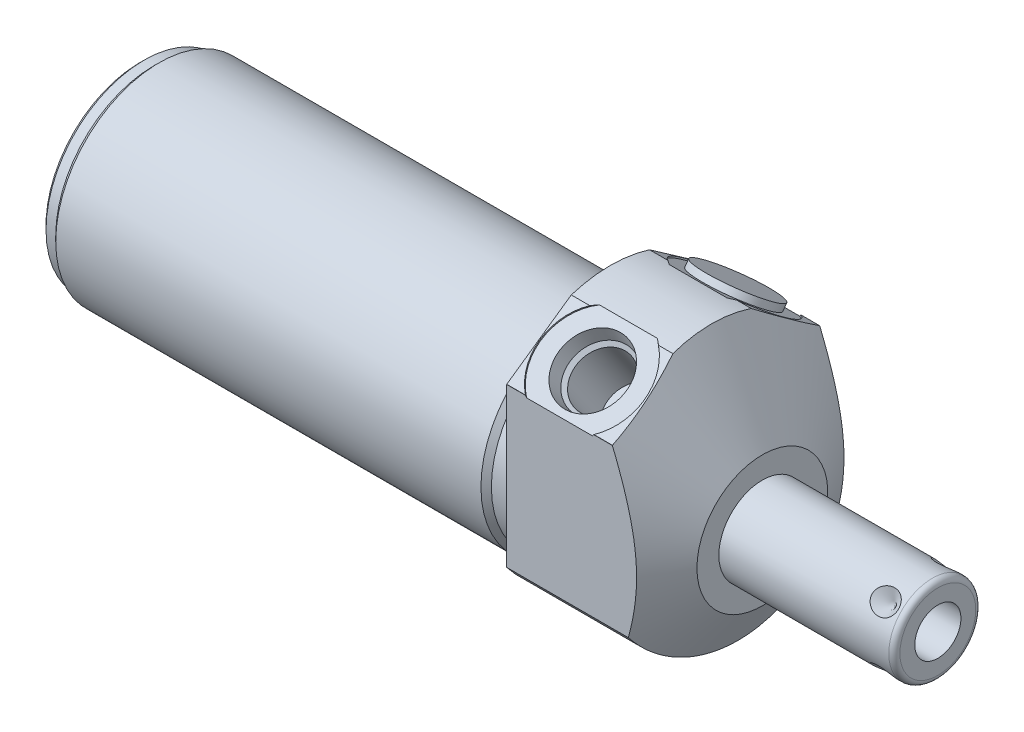
SolidWorks part; units mm, degrees
material "Alloy Steel"
ref_plane "Front Plane" through (0, 0, 0) normal (0, 0, 1) x (1, 0, 0)
ref_plane "Top Plane" through (0, 0, 0) normal (0, 1, 0) x (1, 0, 0)
ref_plane "Right Plane" through (0, 0, 0) normal (1, 0, 0) x (0, 0, -1)
ref_plane "Plane1" through (0, 0, 0) normal (1, 0, 0) x (0, 0, -1)
sketch "Sketch1" plane through (0, 0, 0) normal (1, 0, 0) x (0, 0, -1)
  circle A0 centre (0, 0) radius 23.8125
  dimension "D1" = 47.625
extrude "Extrude1" add sketch "Sketch1" along normal blind 27.7368 and the other way blind 85.852
ref_plane "Plane2" through (0, 0, 0) normal (1, 0, 0) x (0, 0, -1)
sketch "Sketch2" plane through (0, 0, 0) normal (1, 0, 0) x (0, 0, -1)
  line L0 (-20.7455, -4.191) -> (20.7455, -4.191) construction
  circle A0 centre (0, -4.191) radius 18.8595
  circle A1 centre (0, 0) radius 23.8125 construction
  circle A2 centre (0, 0) radius 23.8125
  dimension "D2" = 37.719
  dimension "D1" = 4.191
extrude "Cut-Extrude1" cut sketch "Sketch2" against normal up to next
ref_plane "Plane4" through (0, 0, 0) normal (-1, 0, 0) x (0, 0, 1)
sketch "Sketch4" plane through (0, 0, 0) normal (-1, 0, 0) x (0, 0, 1)
  line L0 (18.923, -14.4553) -> (18.923, 14.4659)
  line L1 (18.923, 14.4659) -> (0, 27.7159)
  line L2 (-18.923, -14.4553) -> (-18.923, 14.4659)
  line L3 (-18.923, 14.4659) -> (0, 27.7159)
  line L4 (0, -26.3889) -> (0, 30.2923) construction
  circle A0 centre (0, 0) radius 28.575
  circle A1 centre (0, 0) radius 23.8125 construction
  arc A3 (-18.923, -14.4553) -> (18.923, -14.4553) centre (0, 0) ccw
  dimension "D4" = 57.15
  dimension "D1" = 37.846
  dimension "D2" = 27.7159
  dimension "D3" = 55
extrude "Cut-Extrude3" cut sketch "Sketch4" against normal up to next
ref_plane "Plane6" through (0, 0, 0) normal (0, 0, 1) x (1, 0, 0)
sketch "Sketch6" plane through (0, 0, 0) normal (0, 0, 1) x (1, 0, 0)
  line L0 (4.7132, 47.625) -> (27.7368, 7.747)
  line L1 (3.6128, -4.191) -> (28.9388, -4.191) construction
  line L2 (-85.852, -4.191) -> (0, -4.191) construction
  line L3 (27.7368, 7.747) -> (27.7368, 47.625)
  line L4 (27.7368, 47.625) -> (4.7132, 47.625)
  line L5 (27.7368, -14.4553) -> (27.7368, 14.4553) construction
  dimension "D1" = 23.876
  dimension "D2" = 30
  dimension "D3" = 39.878
revolve "Cut-Revolve2" cut sketch "Sketch6" angle 360 about L1
ref_plane "Plane7" through (9.652, 18.3948, 12.869) normal (1, 0, 0) x (0, 0.5736, -0.8192)
sketch "S2D0002" plane through (9.652, 18.3948, 12.869) normal (1, 0, 0) x (0, 0.5736, -0.8192)
  line L0 (0, 0) -> (6.1849, 0)
  line L1 (6.1849, 0) -> (5.6423, -2.5527)
  line L2 (5.6423, -2.5527) -> (4.9784, -3.2166)
  line L3 (4.9784, -3.2166) -> (4.9784, -13.462)
  line L4 (4.9784, -13.462) -> (0, -13.462)
  line L5 (0, -13.462) -> (0, 0)
  line L6 (0, -14.1351) -> (0, 0.6731) construction
  dimension "D1" = 13.462
revolve "Cut-Revolve3" cut sketch "S2D0002" angle 360 about L6
ref_plane "Plane8" through (9.652, 18.3948, -12.869) normal (1, 0, 0) x (0, -0.5736, -0.8192)
sketch "Sketch8" plane through (9.652, 18.3948, -12.869) normal (1, 0, 0) x (0, -0.5736, -0.8192)
  line L0 (0, 0) -> (6.1849, 0)
  line L1 (6.1849, 0) -> (5.6423, -2.5527)
  line L2 (5.6423, -2.5527) -> (4.9784, -3.2166)
  line L3 (4.9784, -3.2166) -> (4.9784, -13.462)
  line L4 (4.9784, -13.462) -> (0, -13.462)
  line L5 (0, -13.462) -> (0, 0)
  line L6 (0, -14.1351) -> (0, 0.6731) construction
  dimension "D1" = 13.462
revolve "Cut-Revolve4" cut sketch "Sketch8" angle 360 about L6
sketch "Sketch18" plane through (0, 18.5976, 13.0222) normal (0, 0.8192, 0.5736) x (1, 0, 0)
  circle A0 centre (9.652, 0.0091) radius 9.525
  dimension "D1" = 19.05
extrude "Cut-Extrude4" cut sketch "Sketch18" against normal blind 0.254
sketch "Sketch19" plane through (0, 18.5976, -13.0222) normal (0, 0.8192, -0.5736) x (1, 0, 0)
  circle A0 centre (9.652, -0.0091) radius 9.525
  dimension "D1" = 19.05
extrude "Cut-Extrude5" cut sketch "Sketch19" against normal blind 0.254
ref_plane "Plane10" through (0, 0, 0) normal (0, 0, 1) x (1, 0, 0)
sketch "Sketch10" plane through (0, 0, 0) normal (0, 0, 1) x (1, 0, 0)
  line L0 (0, 14.6685) -> (0, 13.716)
  line L1 (0, 13.716) -> (-3.81, 13.716)
  line L2 (-3.81, 13.716) -> (-4.7625, 14.6685)
  line L3 (-5.0006, -4.191) -> (0.2381, -4.191) construction
  line L4 (0, 14.6685) -> (-4.7625, 14.6685)
  line L5 (-85.852, -4.191) -> (0, -4.191) construction
  line L6 (0, 14.6685) -> (-85.852, 14.6685) construction
  line L7 (0, 14.6685) -> (0, -23.0505) construction
  dimension "D1" = 35.814
  dimension "D2" = 3.81
  dimension "D3" = 45
revolve "Cut-Revolve6" cut sketch "Sketch10" angle 360 about L3
ref_plane "Plane12" through (0, 0, 0) normal (0, 0, 1) x (1, 0, 0)
sketch "Sketch12" plane through (0, 0, 0) normal (0, 0, 1) x (1, 0, 0)
  line L0 (-85.852, 14.6685) -> (-85.852, 13.716)
  line L1 (-85.852, 13.716) -> (-83.312, 13.716)
  line L2 (-83.312, 13.716) -> (-82.3595, 14.6685)
  line L3 (-63.6746, -4.191) -> (-59.8329, -4.191) construction
  line L4 (-85.852, 14.6685) -> (-82.3595, 14.6685)
  line L6 (-85.852, -4.191) -> (-4.7625, -4.191) construction
  line L7 (-4.7625, 14.6685) -> (-85.852, 14.6685) construction
  line L8 (-85.852, 14.6685) -> (-85.852, -23.0505) construction
  dimension "D1" = 35.814
  dimension "D2" = 2.54
  dimension "D3" = 45
revolve "Cut-Revolve8" cut sketch "Sketch12" angle 360 about L3
chamfer "Chamfer1" distance 0.762 angle 45 1 edges at (-85.852, -4.191, 17.907)
ref_plane "Plane13" through (0, 0, 0) normal (0, 0, 1) x (0, -1, 0)
sketch "Sketch13" plane through (0, 0, 0) normal (0, 0, 1) x (0, -1, 0)
  line L0 (4.191, 27.7368) -> (4.191, 59.7662)
  line L1 (4.191, 59.7662) -> (11.1125, 59.7662)
  line L2 (12.1285, 58.7502) -> (12.1285, 27.7368)
  line L3 (12.1285, 27.7368) -> (4.191, 27.7368)
  line L4 (4.191, 26.4452) -> (4.191, 55.9778) construction
  line L5 (4.191, -82.3595) -> (4.191, -4.7625) construction
  line L6 (16.129, 27.7368) -> (-7.747, 27.7368) construction
  line L7 (14.4553, 0) -> (-14.4553, 0) construction
  arc A0 (12.1285, 58.7502) -> (11.1125, 59.7662) centre (11.1125, 58.7502) ccw
  dimension "D2" = 1.016
  dimension "D1" = 59.7662
  dimension "D3" = 15.875
revolve "Revolve1" add sketch "Sketch13" angle 360 about L4
ref_plane "Plane14" through (54.6354, -8.4074, 0) normal (0, 0, 1) x (0, -1, 0)
sketch "S2D0001" plane through (54.6354, -8.4074, 0) normal (0, 0, 1) x (0, -1, 0)
  line L0 (0, 5.1308) -> (0, -10.1092)
  line L1 (0, -10.1092) -> (-4.2164, -12.6427)
  line L2 (0, 5.1308) -> (-4.2164, 5.1308)
  line L3 (-4.2164, 5.1308) -> (-4.2164, -12.6427)
  line L4 (-4.2164, -18.6621) -> (-4.2164, 0.8887) construction
  line L5 (-4.2164, 4.1148) -> (-4.2164, -26.8986) construction
  line L6 (2.7051, 5.1308) -> (-11.1379, 5.1308) construction
  dimension "D1" = 8.4328
  dimension "D2" = 15.24
  dimension "D3" = 59
revolve "Cut-Revolve9" cut sketch "S2D0001" angle 360 about L4
ref_plane "Plane16" through (50.673, -12.1285, 0) normal (0, 0, 1) x (-1, 0, 0)
ref_plane "Plane17" through (0, -2.0955, -2.0955) normal (0, 0.7071, 0.7071) x (-1, 0, 0)
sketch "Sketch16" plane through (50.673, 1.4217, -5.6127) normal (0, -0.7071, -0.7071) x (-1, 0, 0)
  line L0 (-5.1308, 0) -> (-2.7178, 0)
  line L1 (-2.7178, 0) -> (-5.1308, -2.413)
  line L2 (-5.1308, 0) -> (-5.1308, -2.413)
  line L3 (-5.1308, -5.071) -> (-5.1308, 0.1207) construction
  line L4 (-9.0932, -1.016) -> (-9.0932, -14.859) construction
  line L5 (22.9362, 0) -> (-8.0772, 0) construction
  dimension "D1" = 3.9624
  dimension "D2" = 4.826
  dimension "D3" = 45
revolve "Cut-Revolve10" cut sketch "Sketch16" angle 360 about L3
pattern_circular "CirPattern1" count 4 over 360 about axis through (26.4452, -4.191, 0) along (-1, 0, 0) of "Cut-Revolve10"
sketch "Sketch20" plane through (0, 18.3896, -12.8765) normal (0, 0.8192, -0.5736) x (1, 0, 0)
  circle A0 centre (9.652, -0.0091) radius 6.9469
  dimension "D1" = 13.8938
extrude "Extrude2" add sketch "Sketch20" along normal blind 1.27
sketch "Sketch21" plane through (0, 0, 0) normal (0, 0, 1) x (1, 0, 0)
  line L0 (-85.852, 12.954) -> (-85.852, -21.336) construction
  line L9 (-37.4278, -4.191) -> (-52.7948, -4.191) construction
  line L10 (-71.882, -4.191) -> (-85.852, -4.191)
  line L11 (-71.882, -9.1694) -> (-71.882, -4.191)
  line L12 (-82.6254, -9.1694) -> (-71.882, -9.1694)
  line L13 (-83.2866, -9.8306) -> (-82.6254, -9.1694)
  line L14 (-85.852, -10.3759) -> (-83.2866, -9.8306)
  line L15 (-85.852, -10.3759) -> (-85.852, -4.191)
revolve "Cut-Revolve11" cut sketch "Sketch21" angle 360 about L9
